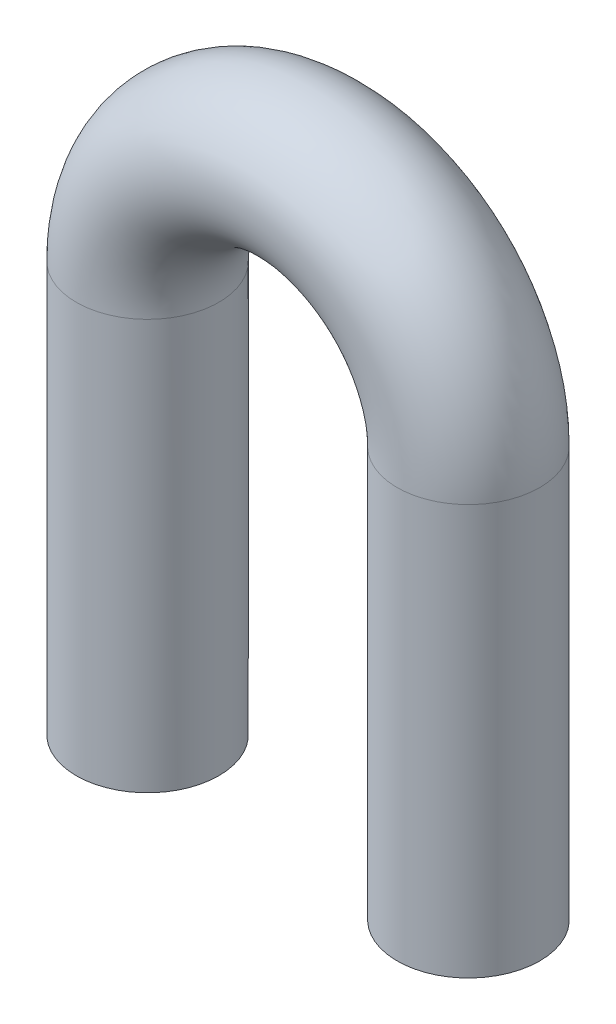
SolidWorks part; units mm, degrees
material "AISI Type A2 Tool Steel"
ref_plane "Front Plane" through (0, 0, 0) normal (0, 0, 1) x (1, 0, 0)
ref_plane "Top Plane" through (0, 0, 0) normal (0, 1, 0) x (1, 0, 0)
ref_plane "Right Plane" through (0, 0, 0) normal (1, 0, 0) x (0, 0, -1)
sketch "Sketch1" plane through (0, 0, 0) normal (0, 1, 0) x (1, 0, 0)
  line L0 (0, -188.2675) -> (0, 9225.1073) construction
  circle A0 centre (4.5, 0) radius 2
  dimension "D2" = 4
  dimension "D1" = 9
revolve "Revolve1" add sketch "Sketch1" angle 180 about L0
sketch "Sketch2" plane through (0, 0, 0) normal (0, -1, 0) x (1, 0, 0)
  circle A0 centre (4.5, 0) radius 2 construction
  circle A1 centre (-4.5, 0) radius 2 construction
  circle A2 centre (4.5, 0) radius 2
  circle A3 centre (-4.5, 0) radius 2
extrude "Boss-Extrude1" add sketch "Sketch2" along normal blind 11.5
